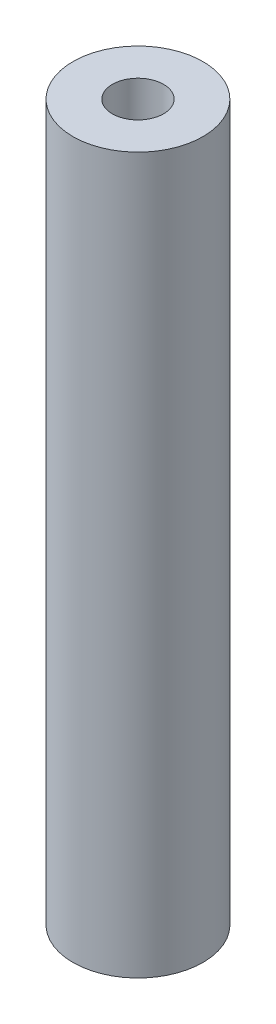
SolidWorks part; units mm, degrees
ref_plane "Front Plane" through (0, 0, 0) normal (0, 0, 1) x (1, 0, 0)
ref_plane "Top Plane" through (0, 0, 0) normal (0, 1, 0) x (1, 0, 0)
ref_plane "Right Plane" through (0, 0, 0) normal (1, 0, 0) x (0, 0, -1)
sketch "Sketch1" plane through (0, 0, 0) normal (0, 1, 0) x (1, 0, 0)
  circle A0 centre (0, 0) radius 3.175
  dimension "D1" = 6.35
extrude "Boss-Extrude1" add sketch "Sketch1" along normal blind 34.925
hole_wizard "M3x0.5 Tapped Hole1" positions "Sketch3" profile "Sketch2" tap size "M3x0.5" standard "ANSI Metric"
sketch "Sketch3" plane through (0, 34.925, 0) normal (0, 1, 0) x (1, 0, 0)
  point P0 (0, 0)
sketch "Sketch2" plane through (0, 34.925, 0) normal (1, 0, 0) x (0, 0, 1)
  line L0 (0, 0) -> (0, 13.4511)
  line L1 (0, 13.4511) -> (1.25, 12.7)
  line L2 (1.25, 12.7) -> (1.25, 0)
  line L5 (1.25, 0) -> (0, 0)
  line L10 (0, 13.4511) -> (-1.25, 12.7) construction
  line L11 (0, -6.35) -> (0, 107.95) construction
  dimension "Tap Drill Dia." = 2.5
  dimension "Tap Drill Depth" = 12.7
  dimension "Drill Angle" = 118
cosmetic thread "Hole Thread1" parameters "D1"=6.096, "D2"=3
hole_wizard "M3x0.5 Tapped Hole2" positions "Sketch5" profile "Sketch4" tap size "M3x0.5" standard "ANSI Metric"
sketch "Sketch5" plane through (0, 0, 0) normal (0, -1, 0) x (-1, 0, 0)
  point P0 (0, 0)
sketch "Sketch4" plane through (0, 0, 0) normal (1, 0, 0) x (0, 0, -1)
  line L0 (0, 0) -> (0, 13.4511)
  line L1 (0, 13.4511) -> (1.25, 12.7)
  line L2 (1.25, 12.7) -> (1.25, 0)
  line L5 (1.25, 0) -> (0, 0)
  line L10 (0, 13.4511) -> (-1.25, 12.7) construction
  line L11 (0, -6.35) -> (0, 107.95) construction
  dimension "Tap Drill Dia." = 2.5
  dimension "Tap Drill Depth" = 12.7
  dimension "Drill Angle" = 118
cosmetic thread "Hole Thread2" parameters "D1"=6.096, "D2"=3
